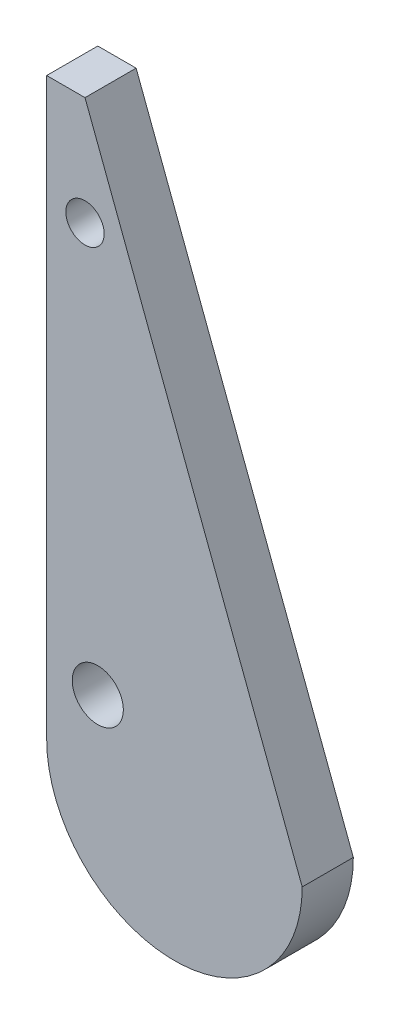
SolidWorks part; units mm, degrees
other "Markup1"
sketch "Sketch3" plane through (0, -10, 4) normal (0, 0, 1) x (1, 0, 0)
other "DetailItem1"
other "DetailItem2"
ref_plane "Front Plane" through (0, 0, 0) normal (0, 0, 1) x (1, 0, 0)
ref_plane "Top Plane" through (0, 0, 0) normal (0, 1, 0) x (1, 0, 0)
ref_plane "Right Plane" through (0, 0, 0) normal (1, 0, 0) x (0, 0, -1)
other "Center of Mass"
sketch "Sketch1" plane through (0, 0, 0) normal (0, 0, 1) x (1, 0, 0)
  line L0 (0, 0) -> (0, 45)
  line L1 (0, 45) -> (3, 45)
  line L2 (3, 45) -> (20, 0)
  arc A0 (0, 0) -> (20, 0) centre (10, 0) ccw
  point P5 (0, 0)
  point P6 (0, 0)
  dimension "D3" = 10
  dimension "D1" = 45
  dimension "D2" = 3
extrude "Boss-Extrude1" add sketch "Sketch1" along normal blind 4
sketch "Sketch2" plane through (0, 0, 4) normal (0, 0, 1) x (1, 0, 0)
  line L0 (0, 45) -> (0, 0) construction
  line L2 (20, 0) -> (3, 45) construction
  circle A0 centre (4, 5) radius 2
  circle A1 centre (3, 36.511) radius 1.5
  point P9 (-3.1309, 41.8085)
  dimension "D2" = 4
  dimension "D3" = 3
  dimension "D1" = 6.8902
  dimension "D4" = 3
  dimension "D5" = 3
  dimension "D6" = 4
  dimension "D7" = 5
extrude "Cut-Extrude1" cut sketch "Sketch2" against normal blind 4
